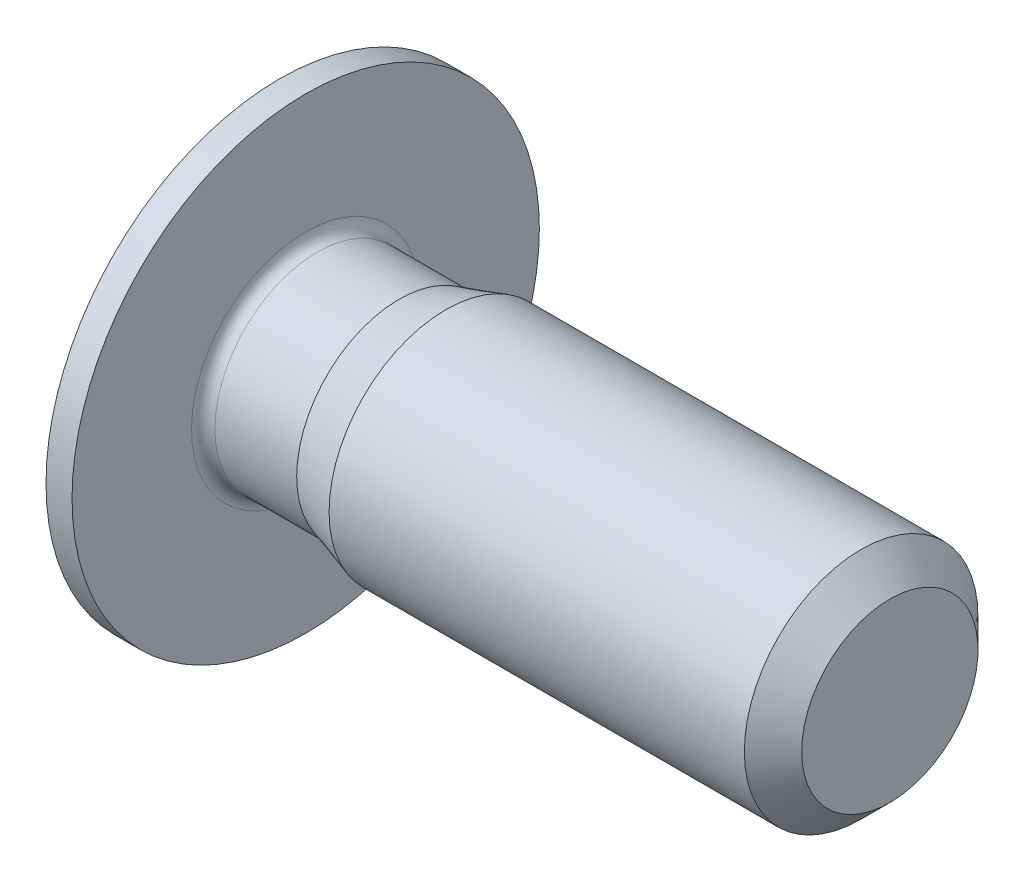
SolidWorks part; units mm, degrees
material "AISI 304"
ref_plane "正面" through (0, 0, 0) normal (0, 0, 1) x (1, 0, 0)
ref_plane "平面" through (0, 0, 0) normal (0, 1, 0) x (1, 0, 0)
ref_plane "右側面" through (0, 0, 0) normal (1, 0, 0) x (0, 0, -1)
ref_plane "Plane1" through (0, 0, 0) normal (0, 0, 1) x (1, 0, 0)
sketch "Sketch1" plane through (0, 0, 0) normal (0, 0, 1) x (1, 0, 0)
  line L0 (-0.5, 0) -> (-0.5, 1.52)
  line L1 (-0.5, 1.52) -> (-0.2229, 2)
  line L2 (-0.2229, 2) -> (0, 2)
  line L3 (0, 2) -> (0, 0.9773)
  line L4 (0.1, 0.8772) -> (0.8, 0.8772)
  line L5 (0.8, 0.8772) -> (1.2, 1)
  line L6 (1.2, 1) -> (4.7545, 1)
  line L7 (4.7545, 1) -> (5, 0.7545)
  line L8 (5, 0.7545) -> (5, 0)
  line L9 (5, 0) -> (-0.5, 0)
  line L10 (5, 0) -> (-0.5, 0) construction
  arc A0 (0, 0.9773) -> (0.1, 0.8772) centre (0.1, 0.9772) ccw
revolve "Revolve1" add sketch "Sketch1" angle 360 about L10
cosmetic thread "Cosmetic Thread1" parameters "D1"=4.8, "D2"=1.509
ref_plane "Plane2" through (0, 0, 0) normal (0, 0, 1) x (1, 0, 0)
sketch "Sketch2" plane through (0, 0, 0) normal (0, 0, 1) x (1, 0, 0)
  line L0 (-0.5, 0) -> (-0.5, 0.65)
  line L1 (-0.5, 0.65) -> (0.7, 0.65)
  line L2 (0.7, 0.65) -> (1.0753, 0)
  line L3 (1.0753, 0) -> (-0.5, 0)
  line L4 (1.0753, 0) -> (-0.5, 0) construction
revolve "Cut-Revolve1" cut sketch "Sketch2" angle 360 about L4
ref_plane "Plane3" through (-0.5, 0, 0) normal (1, 0, 0) x (0, 0, -1)
sketch "Sketch3" plane through (-0.5, 0, 0) normal (1, 0, 0) x (0, 0, -1)
  line L0 (-0.65, -0.3753) -> (0, -0.7506)
  line L1 (0, -0.7506) -> (0.65, -0.3753)
  line L2 (0.65, -0.3753) -> (0.65, 0.3753)
  line L3 (0.65, 0.3753) -> (0, 0.7506)
  line L4 (0, 0.7506) -> (-0.65, 0.3753)
  line L5 (-0.65, 0.3753) -> (-0.65, -0.3753)
extrude "Cut-Extrude1" cut sketch "Sketch3" along normal blind 1.2
